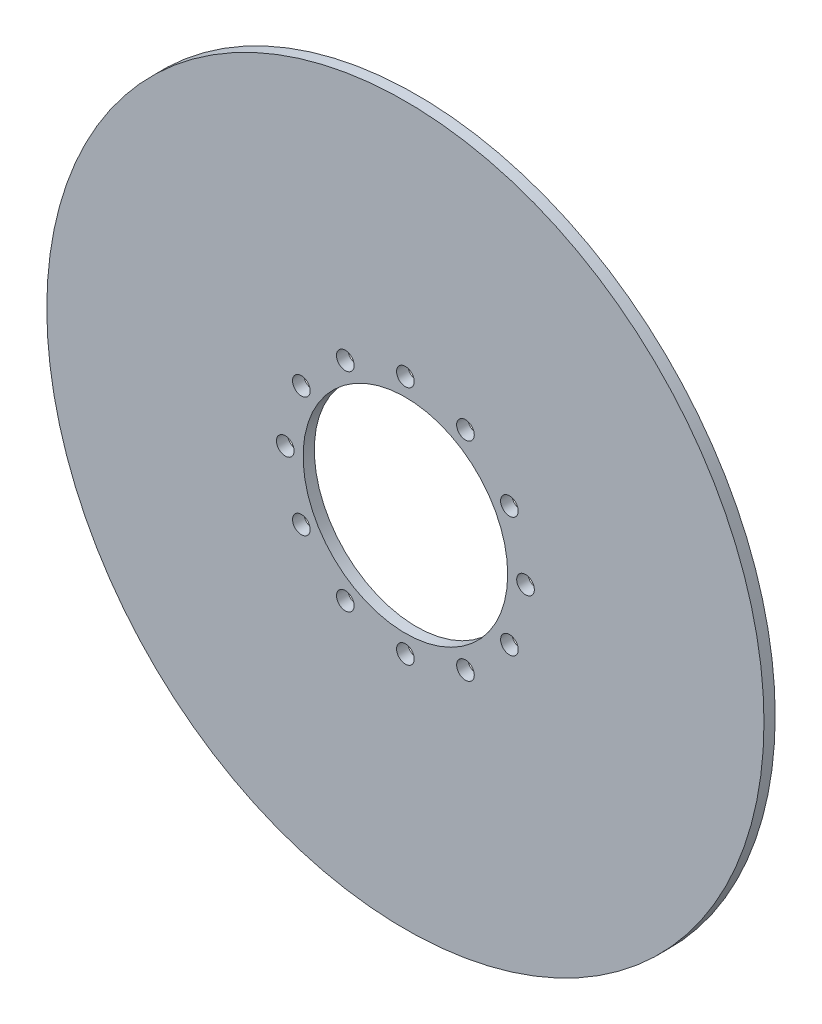
SolidWorks part; units mm, degrees
material "AISI 1020"
ref_plane "Front Plane" through (0, 0, 0) normal (0, 0, 1) x (1, 0, 0)
ref_plane "Top Plane" through (0, 0, 0) normal (0, 1, 0) x (1, 0, 0)
ref_plane "Right Plane" through (0, 0, 0) normal (1, 0, 0) x (0, 0, -1)
sketch "Sketch1" plane through (0, 0, 0) normal (0, 0, 1) x (1, 0, 0)
  circle A0 centre (0, 0) radius 101.5
  circle A1 centre (0, 0) radius 28.956
  circle A2 centre (0, 0) radius 34 construction
  circle A3 centre (0, 34) radius 2.497
  circle A4 centre (17, 29.4449) radius 2.497
  circle A5 centre (29.4449, 17) radius 2.497
  circle A6 centre (34, 0) radius 2.497
  circle A7 centre (29.4449, -17) radius 2.497
  circle A8 centre (17, -29.4449) radius 2.497
  circle A9 centre (0, -34) radius 2.497
  circle A10 centre (-17, -29.4449) radius 2.497
  circle A11 centre (-29.4449, -17) radius 2.497
  circle A12 centre (-34, 0) radius 2.497
  circle A13 centre (-29.4449, 17) radius 2.497
  circle A14 centre (-17, 29.4449) radius 2.497
  point P32 (0, 0)
  dimension "D1" = 203
  dimension "D2" = 57.912
  dimension "D3" = 68
  dimension "D4" = 12
extrude "Boss-Extrude1" add sketch "Sketch1" along normal blind 3.175
move or copy body "Body-Move/Copy2" [suppressed] bodies to move or copy 101
move or copy body "Body-Move/Copy1" [suppressed] bodies to move or copy 101
